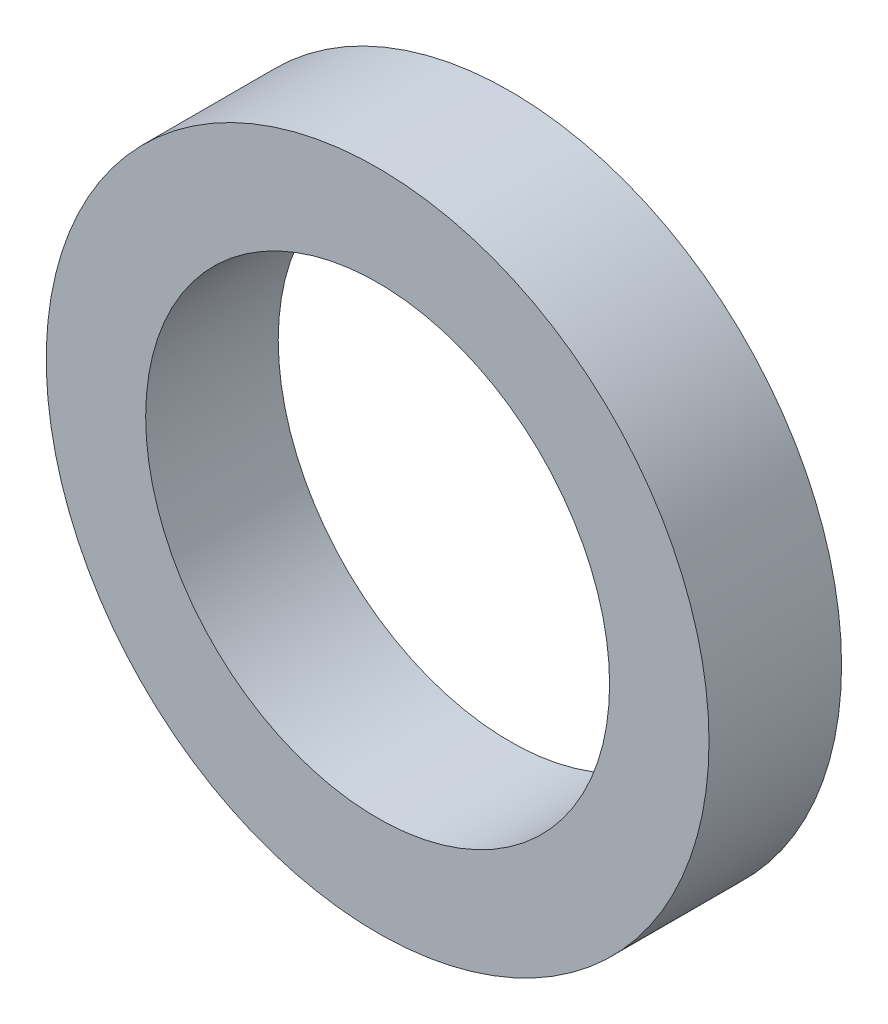
SolidWorks part; units mm, degrees
material "PVC Rigid"
ref_plane "Front Plane" through (0, 0, 0) normal (0, 0, 1) x (1, 0, 0)
ref_plane "Top Plane" through (0, 0, 0) normal (0, 1, 0) x (1, 0, 0)
ref_plane "Right Plane" through (0, 0, 0) normal (1, 0, 0) x (0, 0, -1)
sketch "Sketch1" plane through (0, 0, 0) normal (0, 0, 1) x (1, 0, 0)
  circle A0 centre (0, 0) radius 7
  circle A1 centre (0, 0) radius 10
  dimension "D1" = 14
  dimension "D2" = 20
extrude "Boss-Extrude1" add sketch "Sketch1" along normal blind 4
